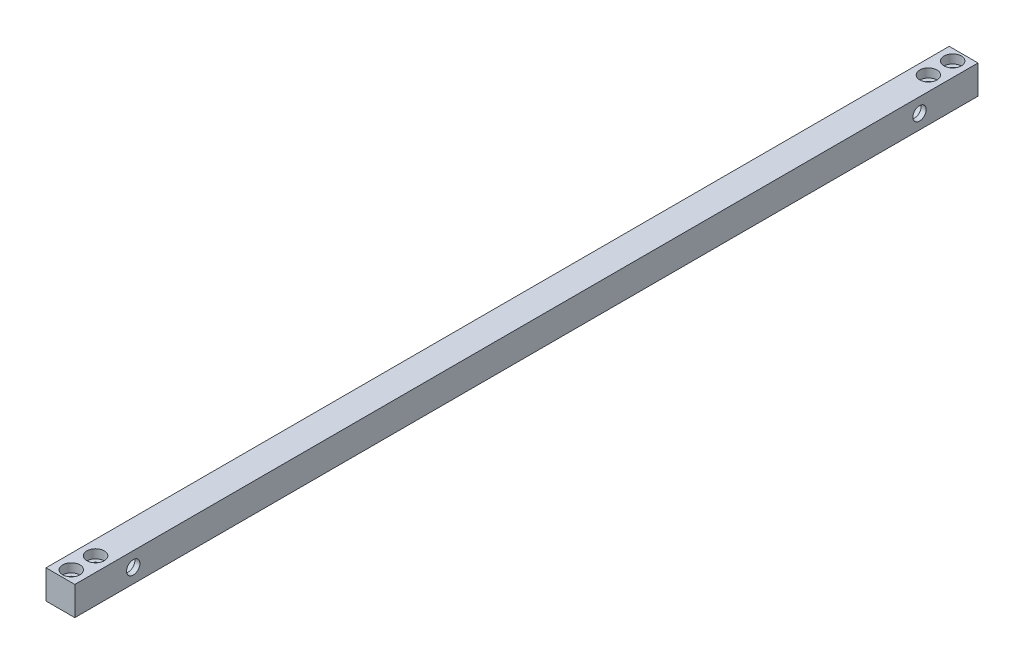
SolidWorks part; units mm, degrees
ref_plane "Front Plane" through (0, 0, 0) normal (0, 0, 1) x (1, 0, 0)
ref_plane "Top Plane" through (0, 0, 0) normal (0, 1, 0) x (1, 0, 0)
ref_plane "Right Plane" through (0, 0, 0) normal (1, 0, 0) x (0, 0, -1)
sketch "Sketch1" plane through (0, 0, 0) normal (0, 0, 1) x (1, 0, 0)
  line L1 (0, 0) -> (15.875, 0)
  line L2 (0, 0) -> (0, 15.875)
  line L3 (0, 15.875) -> (15.875, 15.875)
  line L4 (15.875, 0) -> (15.875, 15.875)
  dimension "D1" = 15.875
  dimension "D2" = 15.875
extrude "Boss-Extrude1" add sketch "Sketch1" along normal blind 497.84
sketch "Sketch8" plane through (0, 0, 0) normal (-1, 0, 0) x (0, 0, 1)
  line L0 (497.84, 7.9375) -> (0, 7.9375) construction
  line L1 (497.84, 15.875) -> (497.84, 0) construction
  line L2 (0, 15.875) -> (0, 0) construction
  line L3 (248.92, 15.875) -> (248.92, 0) construction
  line L4 (497.84, 15.875) -> (0, 15.875) construction
  line L5 (497.84, 0) -> (0, 0) construction
  circle A0 centre (465.6201, 7.9375) radius 6.8199
  circle A1 centre (32.2199, 7.9375) radius 6.8199
  dimension "D1" = 32.2199
extrude "Cut-Extrude1" cut sketch "Sketch8" against normal blind 13.0861
hole_wizard "L (0.29) Diameter Hole1" positions "Sketch10" profile "Sketch9" hole size "L" standard "ANSI Inch"
sketch "Sketch10" plane through (13.0861, 0, 0) normal (-1, 0, 0) x (0, 0, 1)
  point P0 (32.2199, 7.9375)
  point P3 (465.6201, 7.9375)
sketch "Sketch9" plane through (13.0861, 7.9375, 32.2199) normal (0, 1, 0) x (0, 0, 1)
  line L0 (0, 0) -> (0, 53.013)
  line L1 (0, 53.013) -> (3.683, 50.8)
  line L2 (3.683, 50.8) -> (3.683, 0)
  line L5 (3.683, 0) -> (0, 0)
  line L10 (0, 53.013) -> (-3.683, 50.8) construction
  line L11 (0, -6.35) -> (0, 107.95) construction
  dimension "Hole Dia." = 7.366
  dimension "Hole Depth" = 50.8
  dimension "Drill Angle" = 118
hole_wizard "CBORE for #10 Socket Head Cap Screw1" positions "Sketch11" profile "Sketch12" counterbore size "#10" standard "ANSI Inch"
sketch "Sketch11" plane through (412.8741, 15.875, -1707.9731) normal (0, 1, 0) x (1, 0, 0)
  point P0 (-404.9366, -2199.8131)
  point P3 (-404.9366, -2186.4131)
  point P6 (-871.6616, -2186.4131)
  point P9 (-871.6616, -2199.8131)
sketch "Sketch12" plane through (7.9375, 15.875, 491.84) normal (1, 0, 0) x (0, 0, 1)
  line L0 (0, 0) -> (0, 26.8957)
  line L1 (0, 26.8957) -> (2.4892, 25.4)
  line L2 (2.4892, 25.4) -> (2.4892, 4.826)
  line L3 (2.4892, 4.826) -> (4.7625, 4.826)
  line L4 (4.7625, 4.826) -> (4.7625, 0)
  line L5 (4.7625, 0) -> (0, 0)
  line L6 (0, 26.8957) -> (-2.4892, 25.4) construction
  line L7 (0, -6.35) -> (0, 107.95) construction
  dimension "Hole Dia." = 4.9784
  dimension "Hole Depth" = 25.4
  dimension "C'Bore Dia." = 9.525
  dimension "C'Bore Depth" = 4.826
  dimension "Drill Angle" = 118
hole_wizard "CBORE for #10 Socket Head Cap Screw2" positions "Sketch13" profile "Sketch14" counterbore size "#10" standard "ANSI Inch"
sketch "Sketch13" plane through (412.8741, 15.875, -1707.9731) normal (0, 1, 0) x (1, 0, 0)
  point P0 (-404.9366, -1713.9731)
  point P3 (-404.9366, -1727.3731)
  point P6 (-871.6616, -1713.9731)
  point P9 (-871.6616, -1727.3731)
sketch "Sketch14" plane through (7.9375, 15.875, 6) normal (1, 0, 0) x (0, 0, 1)
  line L0 (0, 0) -> (0, 26.8957)
  line L1 (0, 26.8957) -> (2.4892, 25.4)
  line L2 (2.4892, 25.4) -> (2.4892, 4.826)
  line L3 (2.4892, 4.826) -> (4.7625, 4.826)
  line L4 (4.7625, 4.826) -> (4.7625, 0)
  line L5 (4.7625, 0) -> (0, 0)
  line L6 (0, 26.8957) -> (-2.4892, 25.4) construction
  line L7 (0, -6.35) -> (0, 107.95) construction
  dimension "Hole Dia." = 4.9784
  dimension "Hole Depth" = 25.4
  dimension "C'Bore Dia." = 9.525
  dimension "C'Bore Depth" = 4.826
  dimension "Drill Angle" = 118
